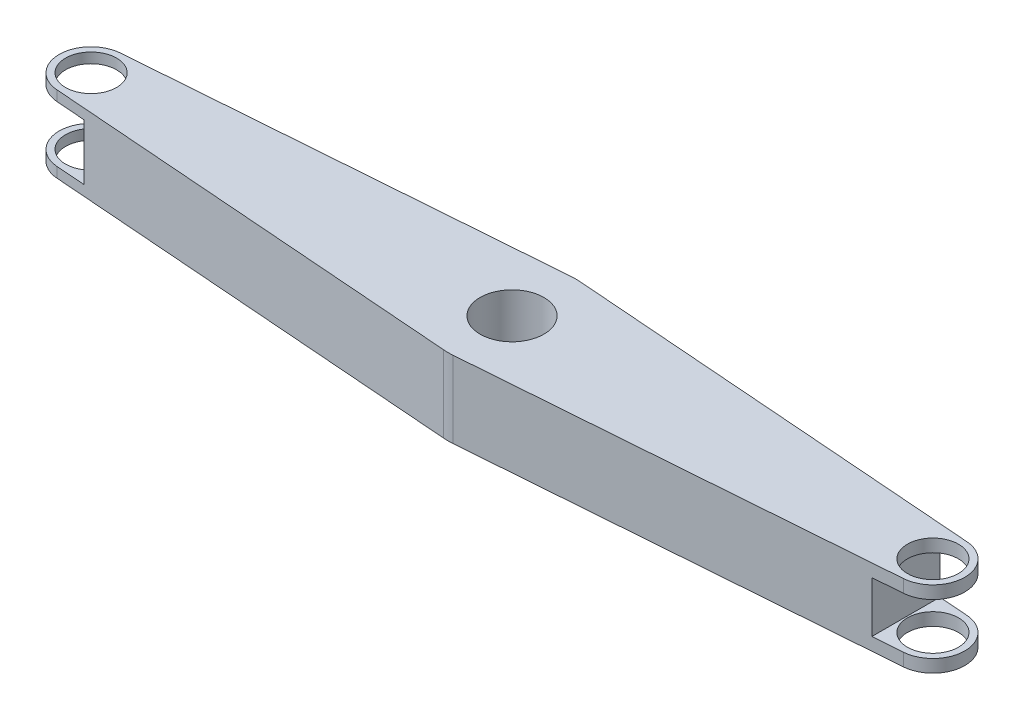
SolidWorks part; units mm, degrees
ref_plane "Alzado" through (0, 0, 0) normal (0, 0, 1) x (1, 0, 0)
ref_plane "Planta" through (0, 0, 0) normal (0, 1, 0) x (1, 0, 0)
ref_plane "Vista lateral" through (0, 0, 0) normal (1, 0, 0) x (0, 0, -1)
sketch "Croquis1" plane through (0, 0, 0) normal (0, 1, 0) x (1, 0, 0)
  line L0 (-165, 0) -> (165, 0) construction
  line L1 (-165.947, 12.4641) -> (-1.8939, 24.9282)
  line L2 (-165.947, -12.4641) -> (-1.8939, -24.9282)
  line L3 (0, 0) -> (0, 42.1122) construction
  line L4 (165.947, -12.4641) -> (1.8939, -24.9282)
  line L5 (165.947, 12.4641) -> (1.8939, 24.9282)
  circle A0 centre (0, 0) radius 12.5
  arc A1 (-1.8939, -24.9282) -> (1.8939, -24.9282) centre (0, 0) ccw
  arc A2 (-165.947, 12.4641) -> (-165.947, -12.4641) centre (-165, 0) ccw
  arc A3 (165.947, -12.4641) -> (165.947, 12.4641) centre (165, 0) ccw
  arc A4 (1.8939, 24.9282) -> (-1.8939, 24.9282) centre (0, 0) ccw
  point P7 (0, 0)
  dimension "D1" = 25
  dimension "D2" = 50
  dimension "D4" = 25
  dimension "D3" = 330
extrude "Saliente-Extruir1" add sketch "Croquis1" along normal mid plane 30
sketch "Croquis2" plane through (0, 0, 0) normal (0, 0, 1) x (1, 0, 0)
  line L0 (-165.947, 0) -> (165.947, 0) construction
  line L1 (165.947, 15) -> (165.947, -15) construction
  line L2 (177.5, -15) -> (177.5, 15) construction
  line L3 (154.3939, -10) -> (177.5, -10)
  line L4 (154.3939, -10) -> (154.3939, 10)
  line L5 (154.3939, 10) -> (177.5, 10)
  line L6 (177.5, -10) -> (177.5, 10)
  line L7 (154.3939, -10) -> (177.5, 10) construction
  line L8 (154.3939, 10) -> (177.5, -10) construction
  line L9 (-177.5, 15) -> (-177.5, -15) construction
  line L10 (-154.3939, -11) -> (-177.5, -11)
  line L11 (-154.3939, -11) -> (-154.3939, 11)
  line L12 (-154.3939, 11) -> (-177.5, 11)
  line L13 (-177.5, -11) -> (-177.5, 11)
  line L14 (-154.3939, -11) -> (-177.5, 11) construction
  line L15 (-154.3939, 11) -> (-177.5, -11) construction
  point P6 (0, 0)
  dimension "D1" = 20
  dimension "D2" = 22
extrude "Cortar-Extruir1" cut sketch "Croquis2" against normal through all both and the other way through all
sketch "Croquis3" plane through (0, 0, 0) normal (0, 1, 0) x (1, 0, 0)
  circle A0 centre (-165, 0) radius 10
  circle A1 centre (165, 0) radius 10
  dimension "D1" = 20
extrude "Cortar-Extruir2" cut sketch "Croquis3" against normal through all both and the other way through all
